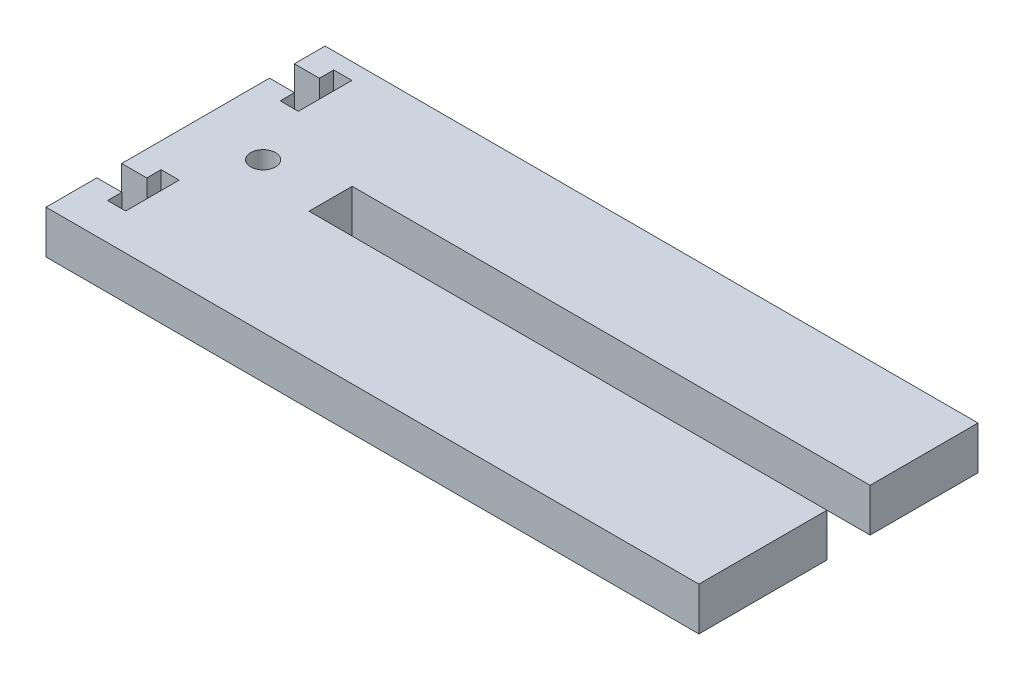
SolidWorks part; units mm, degrees
ref_plane "Front Plane" through (0, 0, 0) normal (0, 0, 1) x (1, 0, 0)
ref_plane "Top Plane" through (0, 0, 0) normal (0, 1, 0) x (1, 0, 0)
ref_plane "Right Plane" through (0, 0, 0) normal (1, 0, 0) x (0, 0, -1)
sketch "Sketch1" plane through (0, 0, 0) normal (0, 1, 0) x (1, 0, 0)
  line L0 (-38.1, 57.15) -> (-38.1, -76.2) construction
  line L1 (-48.0314, 76.2) -> (48.0314, 76.2)
  line L2 (-48.0314, 76.2) -> (-48.0314, 71.6788)
  line L3 (-48.0314, -76.2) -> (48.0314, -76.2)
  line L4 (48.0314, 76.2) -> (48.0314, 60.325)
  line L5 (-48.0314, 76.2) -> (48.0314, -76.2) construction
  line L6 (-48.0314, -76.2) -> (48.0314, 76.2) construction
  line L7 (-38.1, 57.15) -> (48.0314, 57.15) construction
  line L8 (48.0314, 60.325) -> (-28.1686, 60.325)
  line L9 (48.0314, 53.975) -> (-28.1686, 53.975)
  line L10 (-28.1686, 60.325) -> (-28.1686, 53.975)
  line L11 (48.0314, 53.975) -> (48.0314, 22.225)
  line L12 (48.0314, 15.875) -> (-28.1686, 15.875)
  line L13 (-28.1686, 22.225) -> (-28.1686, 15.875)
  line L14 (48.0314, 22.225) -> (-28.1686, 22.225)
  line L15 (48.0314, -22.225) -> (-28.1686, -22.225)
  line L16 (-28.1686, -15.875) -> (-28.1686, -22.225)
  line L17 (48.0314, -15.875) -> (-28.1686, -15.875)
  line L18 (48.0314, -60.325) -> (-28.1686, -60.325)
  line L19 (-28.1686, -53.975) -> (-28.1686, -60.325)
  line L20 (48.0314, -53.975) -> (-28.1686, -53.975)
  line L21 (48.0314, 15.875) -> (48.0314, -15.875)
  line L22 (48.0314, -22.225) -> (48.0314, -53.975)
  line L23 (48.0314, -60.325) -> (48.0314, -76.2)
  line L24 (-38.1, 57.15) -> (-38.1, 31.75) construction
  line L25 (-38.1, 44.45) -> (-48.0314, 44.45) construction
  line L26 (-48.0314, 46.2788) -> (-44.3484, 46.2788)
  line L27 (-44.3484, 46.2788) -> (-44.3484, 48.387)
  line L28 (-44.3484, 48.387) -> (-41.6814, 48.387)
  line L29 (-41.6814, 48.387) -> (-41.6814, 40.513)
  line L30 (-44.3484, 40.513) -> (-41.6814, 40.513)
  line L31 (-44.3484, 42.6212) -> (-44.3484, 40.513)
  line L32 (-48.0314, 42.6212) -> (-44.3484, 42.6212)
  line L33 (-48.0314, 8.1788) -> (-44.3484, 8.1788)
  line L34 (-48.0314, 4.5212) -> (-44.3484, 4.5212)
  line L35 (-44.3484, 4.5212) -> (-44.3484, 2.413)
  line L36 (-44.3484, 2.413) -> (-41.6814, 2.413)
  line L37 (-41.6814, 10.287) -> (-41.6814, 2.413)
  line L38 (-44.3484, 10.287) -> (-41.6814, 10.287)
  line L39 (-44.3484, 8.1788) -> (-44.3484, 10.287)
  line L40 (-48.0314, -29.9212) -> (-44.3484, -29.9212)
  line L41 (-48.0314, -33.5788) -> (-44.3484, -33.5788)
  line L42 (-44.3484, -33.5788) -> (-44.3484, -35.687)
  line L43 (-44.3484, -35.687) -> (-41.6814, -35.687)
  line L44 (-41.6814, -27.813) -> (-41.6814, -35.687)
  line L45 (-44.3484, -27.813) -> (-41.6814, -27.813)
  line L46 (-44.3484, -29.9212) -> (-44.3484, -27.813)
  line L47 (-48.0314, 42.6212) -> (-48.0314, 8.1788)
  line L48 (-48.0314, 4.5212) -> (-48.0314, -29.9212)
  line L49 (-48.0314, -33.5788) -> (-48.0314, -76.2)
  line L50 (-48.0314, 71.6788) -> (-44.3484, 71.6788)
  line L51 (-44.3484, 71.6788) -> (-44.3484, 73.787)
  line L52 (-44.3484, 73.787) -> (-41.6814, 73.787)
  line L53 (-41.6814, 65.913) -> (-41.6814, 73.787)
  line L54 (-44.3484, 65.913) -> (-41.6814, 65.913)
  line L55 (-44.3484, 68.0212) -> (-44.3484, 65.913)
  line L56 (-48.0314, 68.0212) -> (-44.3484, 68.0212)
  line L57 (-48.0314, 68.0212) -> (-48.0314, 46.2788)
  circle A0 centre (-38.1, 57.15) radius 1.8288
  circle A1 centre (-38.1, 31.75) radius 1.8288
  circle A2 centre (-38.1, 6.35) radius 1.8288
  circle A3 centre (-38.1, -19.05) radius 1.8288
  point P0 (0, 0)
  point P40 (-41.6814, 44.45)
  dimension "D9" = 3.6576
  dimension "D1" = 152.4
  dimension "D2" = 96.0628
  dimension "D3" = 9.9314
  dimension "D4" = 19.05
  dimension "D6" = 3.175
  dimension "D7" = 76.2
  dimension "D10" = 3.6576
  dimension "D11" = 6.35
  dimension "D12" = 2.667
  dimension "D13" = 7.874
  dimension "D14" = 12.7
  dimension "D5" = 4
  dimension "D8" = 4
  dimension "D15" = 3
extrude "Boss-Extrude1" add sketch "Sketch1" against normal blind 6.35
sketch "Sketch2" plane through (0, 0, 0) normal (0, 1, 0) x (1, 0, 0)
  line L0 (-48.0314, 42.6212) -> (-48.0314, 8.1788) construction
  line L1 (48.0314, -76.2) -> (-48.0314, -76.2)
  line L2 (48.0314, -76.2) -> (48.0314, 35.1374)
  line L3 (48.0314, 35.1374) -> (-48.0314, 35.1374)
  line L4 (-48.0314, -76.2) -> (-48.0314, 35.1374)
extrude "Cut-Extrude1" cut sketch "Sketch2" against normal through all both
